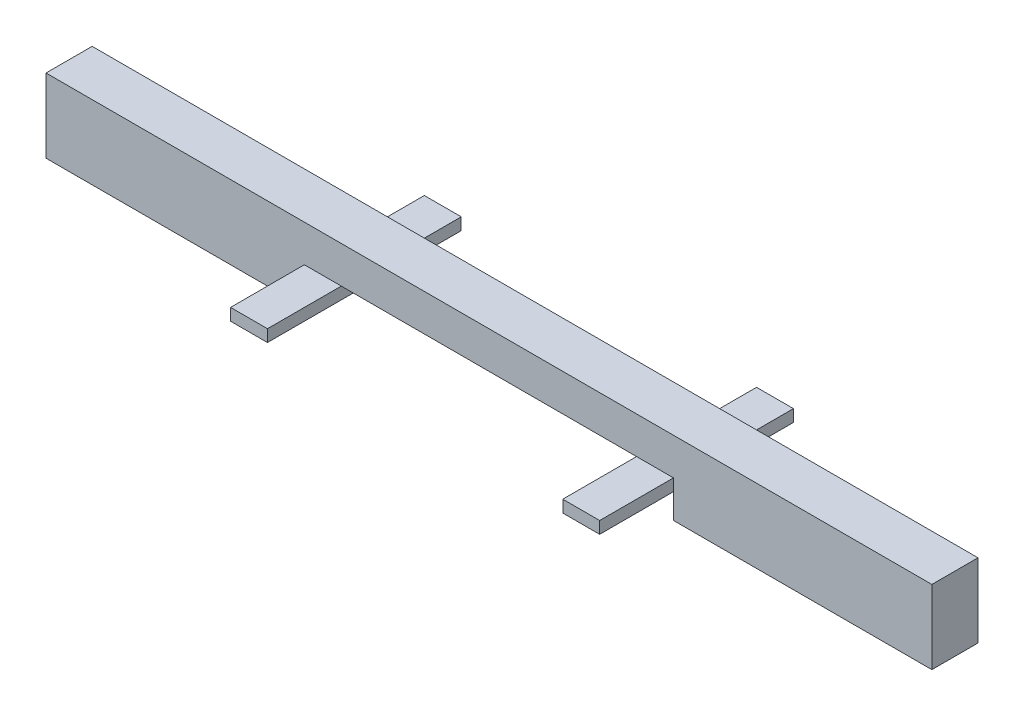
SolidWorks part; units mm, degrees
ref_plane "Front Plane" through (0, 0, 0) normal (0, 0, 1) x (1, 0, 0)
ref_plane "Top Plane" through (0, 0, 0) normal (0, 1, 0) x (1, 0, 0)
ref_plane "Right Plane" through (0, 0, 0) normal (1, 0, 0) x (0, 0, -1)
sketch "Sketch1" plane through (0, 0, 0) normal (0, 0, 1) x (1, 0, 0)
  line L10 (1, 0) -> (9, 0)
  line L12 (0, 1) -> (10, 1)
  line L14 (0, 1) -> (-7, 1)
  line L15 (0, -0.325) -> (0, -1)
  line L16 (0, -1) -> (-7, -1)
  line L17 (-7, 1) -> (-7, -1)
  line L18 (10, 1) -> (17, 1)
  line L19 (10, -0.325) -> (10, -1)
  line L20 (10, -1) -> (17, -1)
  line L21 (17, 1) -> (17, -1)
  line L24 (0, -0.325) -> (1, -0.325)
  line L25 (1, 0) -> (1, -0.325)
  line L28 (10, -0.325) -> (9, -0.325)
  line L29 (9, 0) -> (9, -0.325)
extrude "Boss-Extrude1" add sketch "Sketch1" along normal blind 1.25
sketch "Sketch2" plane through (0, 0, 1.25) normal (0, 0, 1) x (1, 0, 0)
  line L1 (1, -0.325) -> (0, -0.325)
  line L2 (1, -0.325) -> (1, 0)
  line L3 (1, 0) -> (0, 0)
  line L4 (0, -0.325) -> (0, 0)
  line L5 (9, -0.325) -> (10, -0.325)
  line L6 (9, -0.325) -> (9, 0)
  line L7 (9, 0) -> (10, 0)
  line L8 (10, -0.325) -> (10, 0)
  dimension "D1" = 0.325
  dimension "D2" = 1
extrude "Boss-Extrude2" add sketch "Sketch2" along normal blind 2
sketch "Sketch3" plane through (0, 0, 0) normal (0, 0, -1) x (-1, 0, 0)
  line L1 (-9, -0.325) -> (-10, -0.325)
  line L2 (-9, -0.325) -> (-9, 0)
  line L3 (-9, 0) -> (-10, 0)
  line L4 (-10, -0.325) -> (-10, 0)
  line L5 (-1, -0.325) -> (0, -0.325)
  line L6 (-1, -0.325) -> (-1, 0)
  line L7 (-1, 0) -> (0, 0)
  line L8 (0, -0.325) -> (0, 0)
  dimension "D1" = 1
  dimension "D2" = 0.325
  dimension "D3" = 1
  dimension "D4" = 0.325
extrude "Boss-Extrude3" add sketch "Sketch3" along normal blind 2
